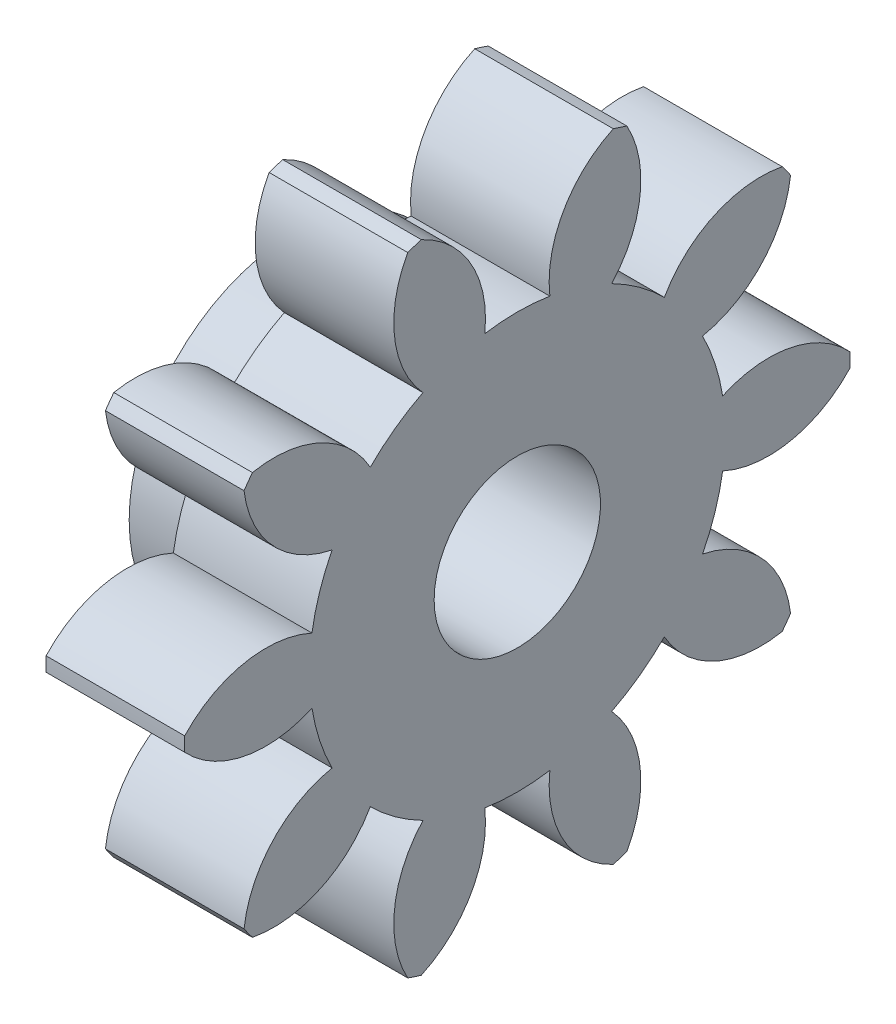
SolidWorks part; units mm, degrees
ref_plane "Plane1" through (0, 0, 0) normal (0, 0, 1) x (1, 0, 0)
ref_plane "Plane2" through (0, 0, 0) normal (0, 1, 0) x (1, 0, 0)
ref_plane "Plane3" through (0, 0, 0) normal (1, 0, 0) x (0, 0, -1)
sketch "HoldingSke" plane through (0, 0, 0) normal (0, 1, 0) x (1, 0, 0)
  line L0 (0, 0) -> (0.4924, -0.0868)
  line L1 (-15, 0) -> (100, 0) construction
  line L2 (0, 0) -> (-2.1039, 2.3779)
  line L3 (0, 0) -> (-11.863, 4.5341)
  line L4 (0, 0) -> (8.5048, 1.4996)
  line L5 (0, 0) -> (-7.4956, -2.7956)
  line L6 (0, 0) -> (-4.1448, -2.7965)
  line L7 (-2.1039, 2.3779) -> (-0.3819, 10.1904)
  line L8 (-76.2, 54.61) -> (-75.2, 54.61)
  line L9 (-71.009, 38.7566) -> (-53.1078, 45.2721)
  line L10 (-76.2, 71.12) -> (104.1128, 71.12)
  line L11 (0, 0) -> (-5, 0)
  line L12 (-76.2, 101.6) -> (-76.133, 101.6)
  line L13 (24.9733, 27.94) -> (52.9518, 28.4284)
  line L14 (24.9733, 27.94) -> (24.9743, 27.94)
  line L15 (24.9733, 27.94) -> (100.4006, 29.5858)
  line L16 (-63.627, -2) -> (-12.827, -2)
  circle A0 centre (0, 0) radius 3
  circle A1 centre (0, 0) radius 6
  circle A2 centre (0, 0) radius 6
  circle A3 centre (0, 0) radius 3
  dimension "MHD" = 12
  dimension "Hub_dia" = 12
  dimension "Bore" = 6
  dimension "MBD" = 6
  dimension "Num_teeth" = 10
  dimension "Pitch" = 0.5
  dimension "Overall_len" = 8
  dimension "Show_teeth" = 10
  dimension "Thickness" = 5
  dimension "OAL" = 8.0001
  dimension "T_dim" = 1
  dimension "Ap" = 20
  dimension "H" = 19.05
  dimension "Pitch_radius" = 180.3128
  dimension "Width" = 5
  dimension "Backlash" = 0.067
  dimension "Addendum_fac" = 1
  dimension "Dedendum_fac" = 1.25
  dimension "Clearance_fac" = 0.25
  dimension "Dedendum_add" = 0.001
  dimension "Module" = 2
sketch "BasProSke" plane through (0, 0, 0) normal (0, 1, 0) x (1, 0, 0)
  line L0 (-10, 0) -> (60, 0) construction
  line L1 (0, 0) -> (0, 12)
  line L2 (0, 0) -> (5, 0)
  line L3 (5, 0) -> (5, 12)
  line L4 (5, 12) -> (0, 12)
  dimension "Thickness" = 5
  dimension "Diameter" = 24
revolve "Base-Revolve" add sketch "BasProSke" angle 360 about L0
sketch "TooCutSke" plane through (0, 0, 0) normal (1, 0, 0) x (0, 0, -1)
  line L1 (0, 0) -> (0, 107) construction
  line L2 (0, 0) -> (-1.6814, 9.8576) construction
  line L3 (0, 0) -> (-6.1153, 18.8209) construction
  line L4 (-1.6814, 9.8576) -> (-3.0576, 9.4105) construction
  arc A0 (1.1737, 7.4066) -> (-1.1737, 7.4066) centre (0, 0) ccw
  arc A1 (3.4979, 11.5054) -> (-3.4979, 11.5054) centre (0, 0) ccw
  circle A2 centre (0, 0) radius 10 construction
  circle A3 centre (0, 0) radius 9.3969 construction
  arc A4 (-1.1737, 7.4066) -> (-3.4979, 11.5054) centre (-5.1477, 7.8615) ccw
  arc A5 (3.4979, 11.5054) -> (1.1737, 7.4066) centre (5.1477, 7.8615) ccw
  dimension "Root_dia" = 14.998
  dimension "Overcut_dia" = 24.0508
  dimension "Pitch_dia" = 20
  dimension "Base_dia" = 18.7939
  dimension "Flank_rad" = 4
  dimension "Half_ang" = 18
  dimension "Half_CT" = 1.4471
extrude "ToothCut" cut sketch "TooCutSke" along normal through all
fillet "Breaks" [suppressed] radius 0.04
fillet "RootFillets" [suppressed] radius 0.501
pattern_circular "TeethCuts" count 10 every 36 about axis through (-10, 0, 0) along (1, 0, 0) of "ToothCut", "RootFillets", "Breaks"
sketch "HubNeaOneSke" plane through (0, 0, 0) normal (-1, 0, 0) x (0, 0, 1)
  circle A0 centre (0, 0) radius 6
  dimension "Diameter" = 12
extrude "HubNearOne" add sketch "HubNeaOneSke" along normal blind 3.0001
sketch "HubNeaBotSke" plane through (0, 0, 0) normal (-1, 0, 0) x (0, 0, 1)
  circle A0 centre (0, 0) radius 6
  dimension "Diameter" = 12
extrude "HubNearBoth" [suppressed] add sketch "HubNeaBotSke" along normal blind 1.5
ref_plane "FarPln" through (5, 0, 0) normal (1, 0, 0) x (0, 0, -1)
sketch "HubFarSke" plane through (5, 0, 0) normal (1, 0, 0) x (0, 0, -1)
  circle A0 centre (0, 0) radius 6
  dimension "Diameter" = 12
extrude "HubFar" [suppressed] add sketch "HubFarSke" along normal blind 1.5
sketch "BorSke" plane through (0, 0, 0) normal (1, 0, 0) x (0, 0, -1)
  circle A0 centre (0, 0) radius 3
  dimension "Diameter" = 6
extrude "Bore" cut sketch "BorSke" along normal mid plane 16.0001
sketch "KeySke" plane through (0, 0, 0) normal (1, 0, 0) x (0, 0, -1)
  line L0 (-1, 0) -> (-1, 4)
  line L1 (-1, 4) -> (1, 4)
  line L2 (1, 4) -> (1, 0)
  line L3 (0, 0) -> (0, 34) construction
  line L4 (-1, 0) -> (1, 0)
  dimension "Offset" = 4
  dimension "Width" = 2
extrude "Keyway" [suppressed] cut sketch "KeySke" along normal mid plane 16.0001
pattern_circular "Keyway2" [suppressed] count 2 every 90 about axis through (-10, 0, 0) along (1, 0, 0)
equation "' \"Module@HoldingSke\" = 6.35"
equation "' \"Num_teeth@HoldingSke\" = 12"
equation "' \"Ap@HoldingSke\" =  20"
equation "' \"Ap@HoldingSke\" = 20"
equation "' \"Width@HoldingSke\" = 0.5 * 25.4"
equation "' \"Hub_dia@HoldingSke\"= 1 * 25.4"
equation "' \"Hub_dia@HoldingSke\" = 1 * 25.4"
equation "' \"Overall_len@HoldingSke\" = 1.0 * 25.4"
equation "' \"Bore@HoldingSke\" = 0.75 * 25.4"
equation "' \"T_dim@HoldingSke\" = 0.1 * 25.4"
equation "' \"Width@KeySke\" = 0.25 * 25.4"
equation "' \"Show_teeth@HoldingSke\" = 13"
equation "' \"Backlash@HoldingSke\" = 0.009 * 25.4"
equation "' \"Addendum_fac@HoldingSke\" = 1.0"
equation "' \"Dedendum_fac@HoldingSke\" = 1.25"
equation "' \"Dedendum_add@HoldingSke\" = 0.00005 * 25.4"
equation "' \"Clearance_fac@HoldingSke\" = 0.25"
equation "\"Pitch@HoldingSke\" = 1 / \"Module@HoldingSke\""
equation "\"Overcut_dia@TooCutSke\" = (\"Num_teeth@HoldingSke\" + 2 * \"Addendum_fac@HoldingSke\") / \"Pitch@HoldingSke\" + 0.002 * 25.4"
equation "\"Pitch_dia@TooCutSke\" = \"Num_teeth@HoldingSke\" / \"Pitch@HoldingSke\""
equation "\"Base_dia@TooCutSke\" = \"Num_teeth@HoldingSke\" / \"Pitch@HoldingSke\" * cos((\"Ap@HoldingSke\"  * 3.14159265 / 180))"
equation "\"Root_dia@TooCutSke\" = (\"Num_teeth@HoldingSke\" + 2) / \"Pitch@HoldingSke\" - 2 * (\"Addendum_fac@HoldingSke\" + \"Dedendum_fac@HoldingSke\") / \"Pitch@HoldingSke\" - \"Dedendum_add@HoldingSke\" * 2"
equation "\"Half_ang@TooCutSke\" = 180 / \"Num_teeth@HoldingSke\""
equation "\"Half_CT@TooCutSke\" = \"Num_teeth@HoldingSke\" / \"Pitch@HoldingSke\" * sin((3.14159265 / 2 / \"Num_teeth@HoldingSke\")) / 2 - 7 * \"Backlash@HoldingSke\" / 4"
equation "\"Flank_rad@TooCutSke\" = \"Num_teeth@HoldingSke\" / \"Pitch@HoldingSke\" / 5"
equation "\"Radius@RootFillets\" = \"Clearance_fac@HoldingSke\" / \"Pitch@HoldingSke\" + \"Dedendum_add@HoldingSke\""
equation "\"Break_rad@Breaks\" = 0.02 / \"Pitch@HoldingSke\""
equation "\"Thickness@HoldingSke\" = \"Width@HoldingSke\""
equation "\"OAL@HoldingSke\" = \"Thickness@HoldingSke\""
equation "\"MHD@HoldingSke\" = (\"Num_teeth@HoldingSke\" + 2) / \"Pitch@HoldingSke\" - 2 * (\"Addendum_fac@HoldingSke\" + \"Dedendum_fac@HoldingSke\")  / \"Pitch@HoldingSke\" - \"Dedendum_add@HoldingSke\" * 2"
equation "\"MBD@HoldingSke\" = (\"Num_teeth@HoldingSke\" + 2) / \"Pitch@HoldingSke\" - 2 * (\"Addendum_fac@HoldingSke\" + \"Dedendum_fac@HoldingSke\")  / \"Pitch@HoldingSke\" - \"Dedendum_add@HoldingSke\" * 2 - 0.002 * 25.4"
equation "\"MHD@HoldingSke\" = ((sgn( \"MHD@HoldingSke\" - \"Hub_dia@HoldingSke\" )-1)*( \"MHD@HoldingSke\" - \"Hub_dia@HoldingSke\" ))/-2+ \"Hub_dia@HoldingSke\""
equation "\"MBD@HoldingSke\" = ((sgn( \"MBD@HoldingSke\" - \"Bore@HoldingSke\" )-1)*( \"MBD@HoldingSke\" - \"Bore@HoldingSke\" ))/-2+ \"Bore@HoldingSke\""
equation "\"OAL@HoldingSke\" = ((sgn( \"OAL@HoldingSke\" - \"Overall_len@HoldingSke\" )+1)*( \"OAL@HoldingSke\" - \"Overall_len@HoldingSke\" ))/2 + \"Overall_len@HoldingSke\" + 0.000002 * 25.4"
equation "\"Num_teeth@TeethCuts\" = int( \"Show_teeth@HoldingSke\" ) + 1"
equation "\"Num_teeth@TeethCuts\" = ((sgn( \"Num_teeth@TeethCuts\" - \"Num_teeth@HoldingSke\" )-1)*( \"Num_teeth@TeethCuts\" - \"Num_teeth@HoldingSke\" ))/-2+ \"Num_teeth@HoldingSke\""
equation "\"Num_teeth@TeethCuts\" = ((sgn( \"Num_teeth@TeethCuts\" - 2.0)+1)*( \"Num_teeth@TeethCuts\" - 2.0))/2 +2.0"
equation "\"Angle@TeethCuts\" = 360.0 / \"Num_teeth@HoldingSke\""
equation "\"Diameter@BasProSke\" = (\"Num_teeth@HoldingSke\" + 2 * \"Addendum_fac@HoldingSke\") / \"Pitch@HoldingSke\""
equation "\"Thickness@BasProSke\"  = \"Thickness@HoldingSke\""
equation "' \"Fillet_rad@BasProSke\" =  \"Thickness@HoldingSke\" * 0.05"
equation "' \"Fillet_rad@BasProSke\" = \"Thickness@HoldingSke\" * 0.05"
equation "\"MHD@HoldingSke\" = ((sgn( \"MHD@HoldingSke\" - \"Root_dia@TooCutSke\" )-1)*( \"MHD@HoldingSke\" - \"Root_dia@TooCutSke\" ))/-2+ \"Root_dia@TooCutSke\""
equation "\"Diameter@HubNeaOneSke\" = \"MHD@HoldingSke\""
equation "\"Length@HubNearOne\" = \"OAL@HoldingSke\" - \"Thickness@BasProSke\""
equation "\"Diameter@HubNeaBotSke\" = \"MHD@HoldingSke\""
equation "\"Length@HubNearBoth\" = ( \"OAL@HoldingSke\" - \"Thickness@BasProSke\" ) / 2.0"
equation "\"Thickness@FarPln\" = \"Thickness@BasProSke\""
equation "\"Diameter@HubFarSke\" = \"MHD@HoldingSke\""
equation "\"Length@HubFar\" = ( \"OAL@HoldingSke\" - \"Thickness@BasProSke\" ) / 2.0"
equation "\"Diameter@BorSke\" = \"MBD@HoldingSke\""
equation "\"D1@Bore\" = \"OAL@HoldingSke\" * 2.0"
equation "\"D1@Keyway\" = \"OAL@HoldingSke\" * 2.0"
equation "\"Offset@KeySke\" = \"T_dim@HoldingSke\" + \"MBD@HoldingSke\" / 2.0"
